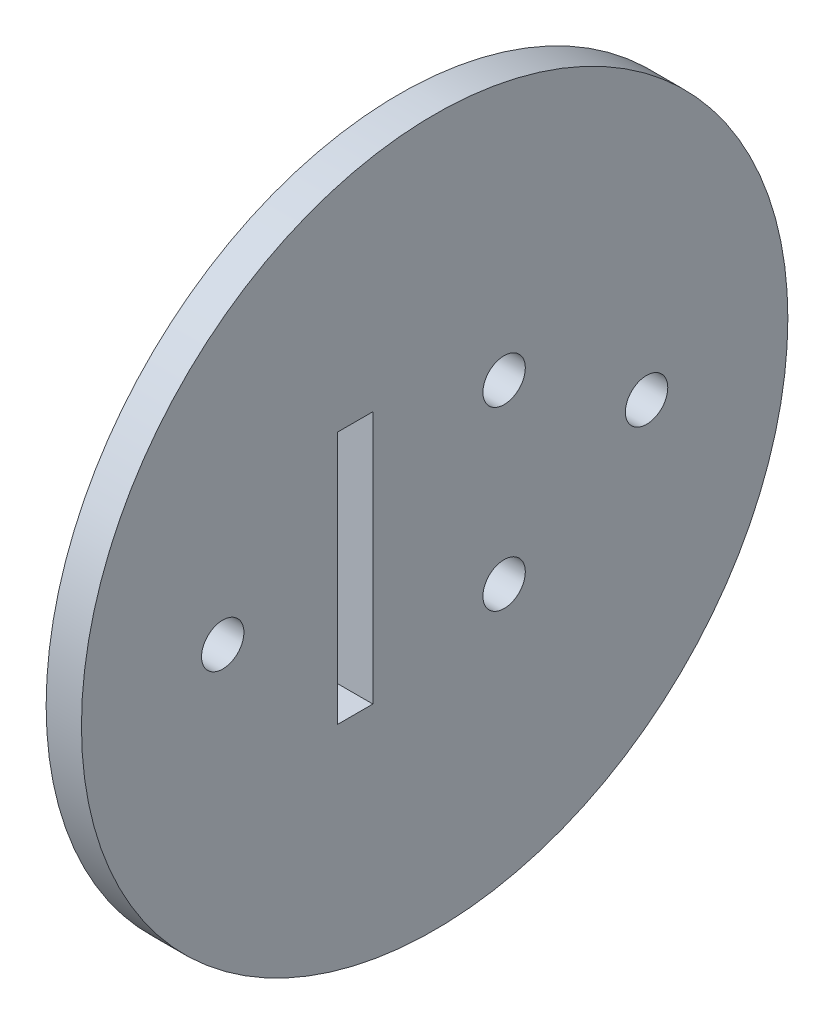
SolidWorks part; units mm, degrees
ref_plane "Front Plane" through (0, 0, 0) normal (0, 0, 1) x (1, 0, 0)
ref_plane "Top Plane" through (0, 0, 0) normal (0, 1, 0) x (1, 0, 0)
ref_plane "Right Plane" through (0, 0, 0) normal (1, 0, 0) x (0, 0, -1)
sketch "Sketch1" plane through (0, 0, 0) normal (1, 0, 0) x (0, 0, -1)
  circle A0 centre (0, 0) radius 30
  dimension "D1" = 60
extrude "Boss-Extrude1" add sketch "Sketch1" along normal blind 3
sketch "Sketch2" plane through (3, 0, 0) normal (1, 0, 0) x (0, 0, -1)
  line L0 (0, 0) -> (18, 0) construction
  line L1 (0, 1.65) -> (0, -1.65) construction
  line L2 (8.25, 10.75) -> (5.9, 10.75) construction
  line L3 (-8.25, 10.75) -> (8.25, 10.75) construction
  line L4 (-8.25, 10.75) -> (-8.25, -10.75) construction
  line L5 (-8.25, -10.75) -> (8.25, -10.75) construction
  line L6 (8.25, 10.75) -> (8.25, -10.75) construction
  line L7 (-8.25, 10.75) -> (8.25, -10.75) construction
  line L8 (-8.25, -10.75) -> (8.25, 10.75) construction
  line L9 (5.9, 10.75) -> (5.9, 7.5) construction
  line L10 (5.9, 7.5) -> (5.9, -7.5) construction
  line L12 (-8.25, 10.75) -> (-5.25, 10.75)
  line L13 (-8.25, 10.75) -> (-8.25, -10.75)
  line L14 (-8.25, -10.75) -> (-5.25, -10.75)
  line L15 (-5.25, 10.75) -> (-5.25, -10.75)
  circle A0 centre (18, 0) radius 1.8
  circle A1 centre (-18, 0) radius 1.8
  circle A2 centre (5.9, 7.5) radius 1.8
  circle A3 centre (5.9, -7.5) radius 1.8
  dimension "D2" = 3.6
  dimension "D8" = 3.6
  dimension "D9" = 3.6
  dimension "D1" = 18
  dimension "D3" = 21.5
  dimension "D4" = 16.5
  dimension "D5" = 2.35
  dimension "D6" = 3.25
  dimension "D7" = 15
  dimension "D11" = 3
extrude "Cut-Extrude1" cut sketch "Sketch2" against normal blind 3
